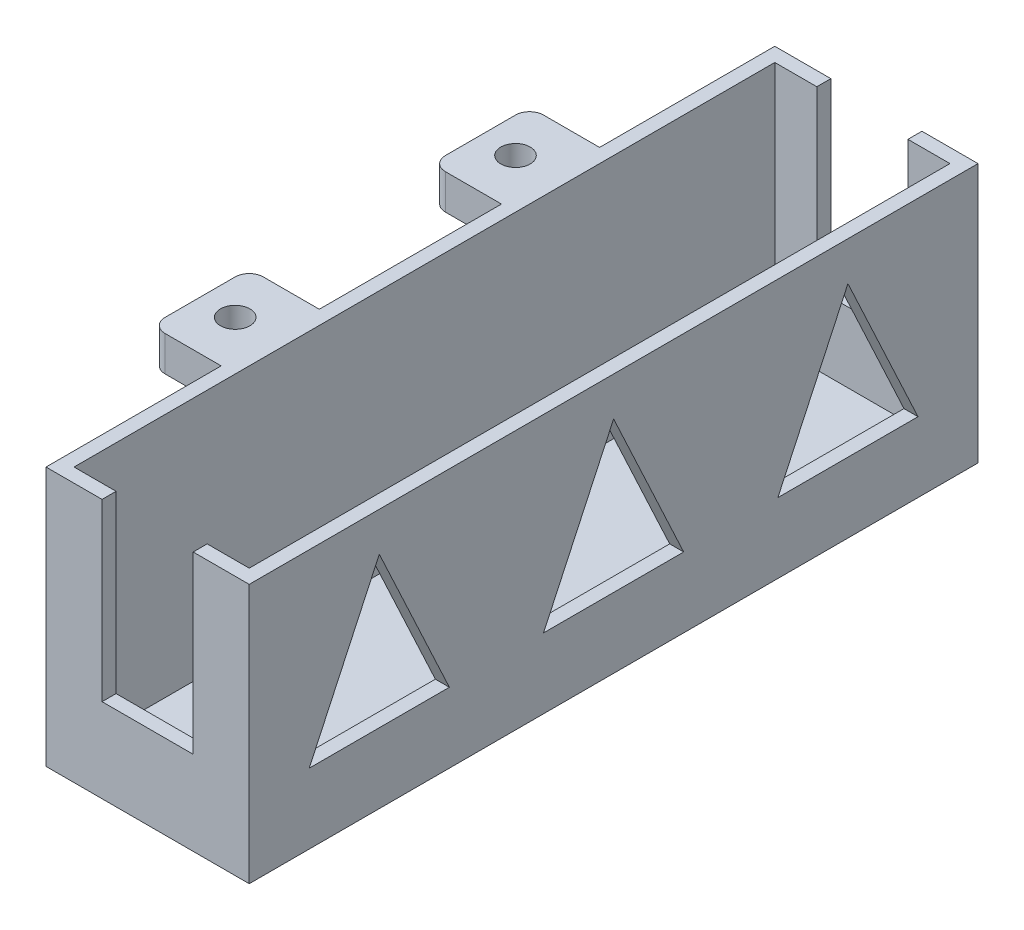
SolidWorks part; units mm, degrees
ref_plane "Front Plane" through (0, 0, 0) normal (0, 0, 1) x (1, 0, 0)
ref_plane "Top Plane" through (0, 0, 0) normal (0, 1, 0) x (1, 0, 0)
ref_plane "Right Plane" through (0, 0, 0) normal (1, 0, 0) x (0, 0, -1)
sketch "Sketch1" plane through (0, 0, 0) normal (0, 1, 0) x (1, 0, 0)
  line L1 (109.4484, -179.3604) -> (119.4484, -179.3604)
  line L2 (109.4484, -179.3604) -> (109.4484, -165.3604)
  line L3 (109.4484, -165.3604) -> (119.4484, -165.3604)
  line L4 (119.4484, -179.3604) -> (119.4484, -165.3604)
  line L5 (109.4484, -179.3604) -> (119.4484, -165.3604) construction
  line L6 (109.4484, -165.3604) -> (119.4484, -179.3604) construction
  line L8 (109.4484, -125.3604) -> (119.4484, -125.3604)
  line L9 (109.4484, -125.3604) -> (109.4484, -139.3604)
  line L10 (109.4484, -139.3604) -> (119.4484, -139.3604)
  line L11 (119.4484, -125.3604) -> (119.4484, -139.3604)
  line L12 (109.4484, -125.3604) -> (119.4484, -139.3604) construction
  line L13 (109.4484, -139.3604) -> (119.4484, -125.3604) construction
  circle A0 centre (114.4484, -172.3604) radius 2.1
  circle A1 centre (114.4484, -132.3604) radius 2.1
  point P0 (114.4484, -172.3604)
  point P8 (114.4484, -132.3604)
  dimension "D1" = 7
  dimension "D2" = 14
sketch "Sketch2" plane through (0, 0, 0) normal (0, 1, 0) x (1, 0, 0)
  line L1 (109.4484, -125.3604) -> (119.4484, -125.3604)
  line L2 (109.4484, -125.3604) -> (109.4484, -139.3604)
  line L3 (109.4484, -139.3604) -> (119.4484, -139.3604)
  line L4 (119.4484, -125.3604) -> (119.4484, -139.3604)
  line L5 (109.4484, -165.3604) -> (119.4484, -165.3604)
  line L6 (109.4484, -165.3604) -> (109.4484, -179.3604)
  line L7 (109.4484, -179.3604) -> (119.4484, -179.3604)
  line L8 (119.4484, -165.3604) -> (119.4484, -179.3604)
  circle A0 centre (114.4484, -132.3604) radius 2.1
  circle A1 centre (114.4484, -172.3604) radius 2.1
extrude "Boss-Extrude1" add sketch "Sketch2" along normal blind 5 contours L6 L5 L8 L7 | L2 L1 L4 L3 | A1 | A0
sketch "Sketch3" plane through (119.4484, 0, 0) normal (1, 0, 0) x (0, 0, -1)
  line L0 (-179.3604, 5) -> (-125.3604, 5) construction
  line L1 (-107.8604, 5) -> (-107.8604, -34)
  line L2 (-107.8604, 5) -> (-196.8604, 5)
  line L3 (-152.3604, 5) -> (-152.3604, -34)
  line L4 (-107.8604, -34) -> (-196.8604, -34)
  line L5 (-196.8604, 5) -> (-196.8604, -34)
  line M6 (-179.3604, 0) -> (-165.3604, 0)
  line M7 (-165.3604, 0) -> (-165.3604, 5)
  line M8 (-165.3604, 5) -> (-179.3604, 5)
  line M9 (-179.3604, 5) -> (-179.3604, 0)
  dimension "D1" = 39
  dimension "D2" = 44.5
extrude "Boss-Extrude2" add sketch "Sketch3" along normal blind 2 contours L2 L5 L4 L3 M7 M6 M9 | L4 L1 L2 L3 | M9 M6 M7 M8
sketch "Sketch4" plane through (121.4484, 0, 0) normal (1, 0, 0) x (0, 0, -1)
  line L0 (-107.8604, -34) -> (-196.8604, -34) construction
  line L1 (-196.8604, 5) -> (-194.8604, 5)
  line L2 (-196.8604, 5) -> (-196.8604, -34)
  line L3 (-196.8604, -34) -> (-194.8604, -34)
  line L4 (-194.8604, 5) -> (-194.8604, -34)
  line L5 (-152.3604, 5) -> (-152.3604, -34) construction
  line L6 (-107.8604, 5) -> (-196.8604, 5) construction
  line L7 (-107.8604, -34) -> (-109.8604, -34)
  line L8 (-109.8604, 5) -> (-109.8604, -34)
  line L9 (-107.8604, 5) -> (-109.8604, 5)
  line L10 (-107.8604, 5) -> (-107.8604, -34)
  line L13 (-194.8604, 5) -> (-194.8604, 3)
  line L15 (-109.8604, 5) -> (-109.8604, 3)
  line L16 (-194.8604, -34) -> (-109.8604, -34)
  line L17 (-194.8604, -34) -> (-194.8604, -32)
  line L18 (-194.8604, -32) -> (-109.8604, -32)
  line L19 (-109.8604, -34) -> (-109.8604, -32)
  line M6 (-107.8604, -34) -> (-107.8604, 5)
  line M7 (-107.8604, 5) -> (-196.8604, 5)
  line M8 (-196.8604, 5) -> (-196.8604, -34)
  line M9 (-196.8604, -34) -> (-107.8604, -34)
  dimension "D1" = 2
  dimension "D2" = 2
  dimension "D3" = 2
extrude "Boss-Extrude4" add sketch "Sketch4" along normal blind 32 contours L5 L18 L4 M9 | L18 L5 L16 L8 | L8 M7 M9 M6 | L4 M7 M8 M9
sketch "Sketch5" plane through (0, -32, 0) normal (0, 1, 0) x (1, 0, 0)
  line L0 (153.4484, -194.8604) -> (121.4484, -194.8604) construction
  line L1 (153.4484, -109.8604) -> (151.4484, -109.8604)
  line L2 (153.4484, -109.8604) -> (153.4484, -194.8604)
  line L3 (153.4484, -194.8604) -> (151.4484, -194.8604)
  line L4 (151.4484, -109.8604) -> (151.4484, -194.8604)
  dimension "D1" = 2
extrude "Boss-Extrude5" add sketch "Sketch5" along normal up to surface (37 mm away) up to face at (125.6984, 5, 152.3604)
sketch "Sketch6" plane through (0, 0, 196.8604) normal (0, 0, 1) x (1, 0, 0)
  line L0 (153.4484, 5) -> (119.4484, 5) construction
  line L1 (129.4484, 5) -> (143.4484, 5)
  line L2 (129.4484, 5) -> (129.4484, -25)
  line L3 (129.4484, -25) -> (143.4484, -25)
  line L4 (143.4484, 5) -> (143.4484, -25)
  line L5 (153.4484, 5) -> (153.4484, -34) construction
  line L6 (119.4484, 5) -> (119.4484, -34) construction
  dimension "D1" = 10
  dimension "D2" = 10
  dimension "D3" = 30
extrude "Cut-Extrude1" cut sketch "Sketch6" against normal blind 200
sketch "Sketch7" plane through (153.4484, 0, 0) normal (1, 0, 0) x (0, 0, -1)
  line L0 (-196.8604, -14.5) -> (-107.8604, -14.5) construction
  line L1 (-196.8604, 5) -> (-196.8604, -34) construction
  line L2 (-107.8604, -34) -> (-107.8604, 5) construction
  line L4 (-189.3604, -24.5) -> (-169.3604, -24.5)
  line L5 (-189.3604, -24.5) -> (-189.3604, -4.5)
  line L6 (-189.3604, -4.5) -> (-169.3604, -4.5)
  line L7 (-169.3604, -24.5) -> (-169.3604, -4.5)
  line L8 (-189.3604, -24.5) -> (-169.3604, -4.5) construction
  line L9 (-189.3604, -4.5) -> (-169.3604, -24.5) construction
  line L10 (-162.3604, -24.5) -> (-142.3604, -24.5)
  line L11 (-162.3604, -24.5) -> (-162.3604, -4.5)
  line L12 (-162.3604, -4.5) -> (-142.3604, -4.5)
  line L13 (-142.3604, -24.5) -> (-142.3604, -4.5)
  line L14 (-162.3604, -24.5) -> (-142.3604, -4.5) construction
  line L15 (-162.3604, -4.5) -> (-142.3604, -24.5) construction
  line L16 (-135.3604, -24.5) -> (-115.3604, -24.5)
  line L17 (-135.3604, -24.5) -> (-135.3604, -4.5)
  line L18 (-135.3604, -4.5) -> (-115.3604, -4.5)
  line L19 (-115.3604, -24.5) -> (-115.3604, -4.5)
  line L20 (-135.3604, -24.5) -> (-115.3604, -4.5) construction
  line L21 (-135.3604, -4.5) -> (-115.3604, -24.5) construction
  point P6 (-179.3604, -14.5)
  point P11 (-152.3604, -14.5)
  point P16 (-125.3604, -14.5)
  dimension "D1" = 7
  dimension "D2" = 20
  dimension "D3" = 20
  dimension "D4" = 20
  dimension "D5" = 20
  dimension "D6" = 20
  dimension "D7" = 20
  dimension "D8" = 7.5
extrude "Cut-Extrude2" cut sketch "Sketch7" against normal blind 16
fillet "Fillet1" radius 2 4 edges at (109.4484, 2.5, 125.3604) (109.4484, 2.5, 139.3604) (109.4484, 2.5, 165.3604) (109.4484, 2.5, 179.3604)
sketch "Sketch8" plane through (153.4484, 0, 0) normal (1, 0, 0) x (0, 0, -1)
  line L1 (-208.3883, 12.4688) -> (-88.7688, 12.4688)
  line L2 (-208.3883, 12.4688) -> (-208.3883, -43.1388)
  line L3 (-208.3883, -43.1388) -> (-88.7688, -43.1388)
  line L4 (-88.7688, 12.4688) -> (-88.7688, -43.1388)
extrude "Cut-Extrude3" cut sketch "Sketch8" against normal up to surface (32 mm away) up to face at (121.4484, -13.5, 152.3604)
sketch "Sketch9" plane through (121.4484, 0, 0) normal (1, 0, 0) x (0, 0, -1)
  line L0 (-152.3604, 5) -> (-152.3604, -34) construction
  line L1 (-107.8604, 5) -> (-196.8604, 5) construction
  line L2 (-107.8604, -34) -> (-196.8604, -34) construction
  line L3 (-102.3604, 5) -> (-102.3604, -30)
  line L4 (-102.3604, 5) -> (-202.3604, 5)
  line L5 (-152.3604, 5) -> (-152.3604, -30)
  line L6 (-102.3604, -30) -> (-202.3604, -30)
  line L7 (-202.3604, 5) -> (-202.3604, -30)
  line M7 (-107.8604, -34) -> (-107.8604, 5)
  line M9 (-196.8604, 5) -> (-196.8604, -34)
  line M10 (-196.8604, -34) -> (-107.8604, -34)
  dimension "D1" = 50
  dimension "D2" = 35
extrude "Boss-Extrude6" add sketch "Sketch9" against normal up to surface (2 mm away) contours L4 L7 L6 M9 | L6 L3 L4 M7 | L6 L5 L4 M9 | L0 L6 M9 M10 | L6 L0 M10 M7 up to face at (119.4484, -3.1667, 152.3604)
sketch "Sketch10" plane through (121.4484, 0, 0) normal (1, 0, 0) x (0, 0, -1)
  line L1 (-196.8604, -30) -> (-107.8604, -30)
  line L2 (-196.8604, -30) -> (-196.8604, -34)
  line L3 (-196.8604, -34) -> (-107.8604, -34)
  line L4 (-107.8604, -30) -> (-107.8604, -34)
extrude "Cut-Extrude4" cut sketch "Sketch10" against normal blind 10
sketch "Sketch11" plane through (121.4484, 0, 0) normal (1, 0, 0) x (0, 0, -1)
  line L1 (-202.3604, 5) -> (-204.3604, 5)
  line L2 (-202.3604, 5) -> (-202.3604, -30)
  line L3 (-202.3604, -30) -> (-204.3604, -30)
  line L4 (-204.3604, 5) -> (-204.3604, -30)
  line L5 (-102.3604, 5) -> (-100.3604, 5)
  line L6 (-102.3604, 5) -> (-102.3604, -30)
  line L7 (-102.3604, -30) -> (-100.3604, -30)
  line L8 (-100.3604, 5) -> (-100.3604, -30)
  line L9 (-204.3604, -30) -> (-100.3604, -30)
  line L10 (-204.3604, -30) -> (-204.3604, -32)
  line L11 (-204.3604, -32) -> (-100.3604, -32)
  line L12 (-100.3604, -30) -> (-100.3604, -32)
  line M4 (-202.3604, 5) -> (-202.3604, -30)
  line M5 (-202.3604, -30) -> (-102.3604, -30)
  dimension "D1" = 2
  dimension "D2" = 2
  dimension "D3" = 2
extrude "Boss-Extrude7" add sketch "Sketch11" along normal blind 25 separate body contours L1 L4 L3 M4 | L12 L7 L3 L10 L11 M5
sketch "Sketch12" plane through (121.4484, 0, 0) normal (-1, 0, 0) x (0, 0, 1)
  line L0 (204.3604, 5) -> (204.3604, -32) construction
  line L1 (100.3604, 5) -> (102.3604, 5)
  line L2 (100.3604, 5) -> (100.3604, -30)
  line L3 (100.3604, -30) -> (102.3604, -30)
  line L4 (102.3604, 5) -> (102.3604, -30)
  line L5 (202.3604, 5) -> (204.3604, 5)
  line L6 (202.3604, 5) -> (202.3604, -30)
  line L7 (202.3604, -30) -> (204.3604, -30)
  line L8 (204.3604, 5) -> (204.3604, -30)
  line L10 (204.3604, -32) -> (100.3604, -32)
  line L11 (204.3604, -32) -> (204.3604, -30)
  line L12 (204.3604, -30) -> (100.3604, -30)
  line L13 (100.3604, -32) -> (100.3604, -30)
  line M1 (204.3604, 5) -> (202.3604, 5)
  line M2 (202.3604, 5) -> (202.3604, -30)
  line M3 (202.3604, -30) -> (102.3604, -30)
  line M4 (102.3604, -30) -> (102.3604, 5)
  line M5 (102.3604, 5) -> (100.3604, 5)
  line M6 (100.3604, 5) -> (100.3604, -32)
  line M7 (100.3604, -32) -> (204.3604, -32)
  line M8 (204.3604, -32) -> (204.3604, 5)
extrude "Boss-Extrude8" add sketch "Sketch12" along normal blind 2 contours L3 M6 M4 M5 | L7 L3 M3 M6 M7 M8 | L7 M2 M8 M1
sketch "Sketch13" plane through (146.4484, 0, 0) normal (1, 0, 0) x (0, 0, -1)
  line L0 (-204.3604, -22) -> (-100.3604, -22) construction
  line L1 (-204.3604, 5) -> (-100.3604, 5)
  line L2 (-204.3604, 5) -> (-204.3604, -32)
  line L3 (-204.3604, -32) -> (-100.3604, -32)
  line L4 (-100.3604, 5) -> (-100.3604, -32)
  line L5 (-195.7981, -22) -> (-175.7981, -22)
  line L6 (-175.7981, -22) -> (-185.7981, -0.5549)
  line L7 (-185.7981, -0.5549) -> (-195.7981, -22)
  line L8 (-152.3604, 5) -> (-152.3604, -32) construction
  line L9 (-128.9227, -22) -> (-118.9227, -0.5549)
  line L10 (-108.9227, -22) -> (-128.9227, -22)
  line L11 (-118.9227, -0.5549) -> (-108.9227, -22)
  line L12 (-162.3604, -22) -> (-142.3604, -22)
  line L13 (-118.9227, -0.5549) -> (-152.3604, -0.5549) construction
  line L14 (-142.3604, -22) -> (-152.3604, -0.5549)
  line L15 (-162.3604, -22) -> (-152.3604, -0.5549)
  point P19 (-152.3604, -22)
  dimension "D1" = 10
  dimension "D2" = 20
  dimension "D3" = 10
  dimension "D4" = 115
  dimension "D5" = 20
extrude "Boss-Extrude9" add sketch "Sketch13" along normal blind 2 contours L2 L1 L4 L3 | L9 L11 L10 | L15 L14 L12 | L7 L5 L6
sketch "Sketch14" plane through (0, 0, 100.3604) normal (0, 0, -1) x (-1, 0, 0)
  line L0 (-133.9484, 5) -> (-133.9484, -32) construction
  line L1 (-119.4484, 5) -> (-148.4484, 5) construction
  line L2 (-119.4484, -32) -> (-148.4484, -32) construction
  line L4 (-140.4484, -10) -> (-127.4484, -10)
  line L5 (-140.4484, -10) -> (-140.4484, 20)
  line L6 (-140.4484, 20) -> (-127.4484, 20)
  line L7 (-127.4484, -10) -> (-127.4484, 20)
  line L8 (-140.4484, -10) -> (-127.4484, 20) construction
  line L9 (-140.4484, 20) -> (-127.4484, -10) construction
  dimension "D1" = 30
  dimension "D2" = 13
extrude "Cut-Extrude5" cut sketch "Sketch14" against normal up to surface (104 mm away) up to face at (133.9484, -13.5, 204.3604)
sketch "Sketch15" plane through (0, 0, 100.3604) normal (0, 0, -1) x (-1, 0, 0)
  line L1 (-140.4484, 5) -> (-127.4484, 5)
  line L2 (-140.4484, 5) -> (-140.4484, -20)
  line L3 (-140.4484, -20) -> (-127.4484, -20)
  line L4 (-127.4484, 5) -> (-127.4484, -20)
  dimension "D1" = 25
extrude "Cut-Extrude7" cut sketch "Sketch15" against normal blind 120
